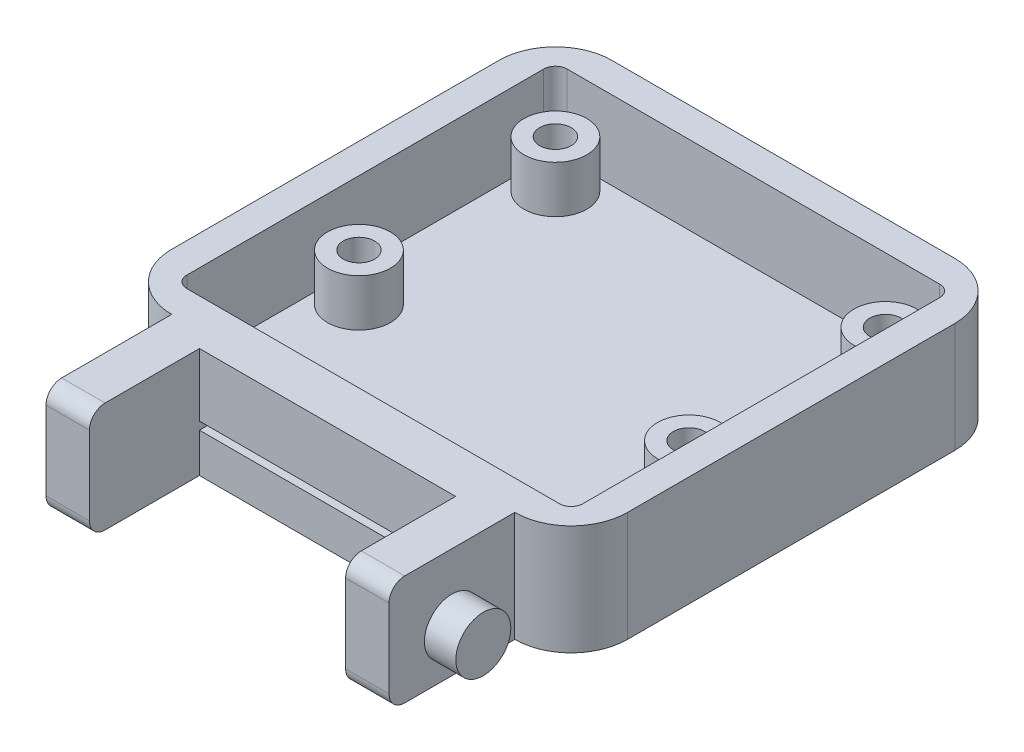
SolidWorks part; units mm, degrees
ref_plane "Front Plane" through (0, 0, 0) normal (0, 0, 1) x (1, 0, 0)
ref_plane "Top Plane" through (0, 0, 0) normal (0, 1, 0) x (1, 0, 0)
ref_plane "Right Plane" through (0, 0, 0) normal (1, 0, 0) x (0, 0, -1)
sketch "Sketch1" plane through (0, 0, 0) normal (0, 1, 0) x (1, 0, 0)
  line L0 (-12.9215, 14.3928) -> (-12.9215, -6.4335)
  line L1 (-9.3347, 17.9797) -> (12.4917, 17.9797)
  line L2 (16.0785, 14.3928) -> (16.0785, -6.4335)
  line L3 (12.4917, -10.0203) -> (-9.3347, -10.0203)
  arc A0 (-12.9215, 14.3928) -> (-9.3347, 17.9797) centre (-9.3347, 14.3928) cw
  arc A1 (12.4917, 17.9797) -> (16.0785, 14.3928) centre (12.4917, 14.3928) cw
  arc A2 (-12.9215, -6.4335) -> (-9.3347, -10.0203) centre (-9.3347, -6.4335) ccw
  arc A3 (16.0785, -6.4335) -> (12.4917, -10.0203) centre (12.4917, -6.4335) cw
  point P12 (13.3502, -6.731)
  point P13 (10.2345, 13.1228)
  point P14 (-14.244, -6.1966)
  point P15 (13.2342, -7.4419)
  point P16 (13.2944, -7.6806)
  point P17 (14.1323, -8.0157)
  point P18 (16.4783, -7.5114)
  point P19 (-10.5014, -10.8645)
  point P20 (16.0873, -8.6844)
  point P21 (16.2549, -8.6753)
  point P22 (-12.4565, 12.2051)
  point P23 (-12.0096, -7.3454)
  dimension "D1" = 29
  dimension "D2" = 28
extrude "Boss-Extrude1" add sketch "Sketch1" along normal blind 7
sketch "Sketch2" plane through (0, 7, 0) normal (0, 1, 0) x (1, 0, 0)
  line L0 (-10.2745, 16.0797) -> (13.4314, 16.0797)
  line L1 (14.1785, 15.3326) -> (14.1785, -7.3733)
  line L2 (13.4314, -8.1203) -> (-10.2745, -8.1203)
  line L4 (-8.9215, 13.9797) -> (12.0785, 13.9797) construction
  line L5 (1.5785, 16.0797) -> (1.5785, -8.1203) construction
  line L6 (-11.0215, -7.3733) -> (-11.0215, 15.3326)
  line L7 (12.4917, 17.9797) -> (-9.3347, 17.9797) construction
  line L8 (16.0785, -6.4335) -> (16.0785, 14.3928) construction
  circle A0 centre (-8.9215, 13.9797) radius 2
  circle A1 centre (12.0785, 13.9797) radius 2
  circle A2 centre (-8.9215, 1.4797) radius 2
  circle A3 centre (12.0785, 1.4797) radius 2
  arc A4 (-10.2745, 16.0797) -> (-11.0215, 15.3326) centre (-10.2745, 15.3326) ccw
  arc A5 (13.4314, 16.0797) -> (14.1785, 15.3326) centre (13.4314, 15.3326) cw
  arc A6 (14.1785, -7.3733) -> (13.4314, -8.1203) centre (13.4314, -7.3733) cw
  arc A7 (-10.2745, -8.1203) -> (-11.0215, -7.3733) centre (-10.2745, -7.3733) cw
  point P22 (0, 0)
  point P23 (0, 0)
  point P24 (0, 0)
  point P25 (1.5785, 13.9797)
  point P26 (0, 0)
  point P31 (-9.6321, 16.0797)
  point P32 (13.4314, -8.1203)
  dimension "D5" = 1.9
  dimension "D7" = 4
  dimension "D1" = 21
  dimension "D2" = 12.5
  dimension "D3" = 24.2
  dimension "D4" = 25.2
  dimension "D6" = 1.9
  dimension "D8" = 2.1
extrude "Cut-Extrude2" cut sketch "Sketch2" against normal blind 5
sketch "Sketch3" plane through (0, 7, 0) normal (0, 1, 0) x (1, 0, 0)
  circle A0 centre (12.0785, 13.9797) radius 2
  circle A1 centre (12.0785, 1.4797) radius 2
  circle A2 centre (-8.9215, 13.9797) radius 2
  circle A3 centre (-8.9215, 1.4797) radius 2
extrude "Cut-Extrude3" cut sketch "Sketch3" against normal blind 2
sketch "Sketch4" plane through (0, 0, 10.0203) normal (0, 0, 1) x (1, 0, 0)
  line L0 (-9.3347, 7) -> (12.4917, 7) construction
  line L1 (9.7285, 3) -> (-6.5715, 3)
  line L2 (9.7285, 3) -> (9.7285, 2.5)
  line L3 (9.7285, 2.5) -> (-6.5715, 2.5)
  line L4 (-6.5715, 3) -> (-6.5715, 2.5)
  line L5 (1.5785, 7) -> (1.5785, 0) construction
  line L6 (-9.3347, 0) -> (12.4917, 0) construction
  point P10 (1.5785, 3)
  dimension "D1" = 4
  dimension "D2" = 16.3
  dimension "D3" = 0.5
extrude "Cut-Extrude4" cut sketch "Sketch4" against normal blind 2
hole_wizard "Ø2.0mm Dowel Hole1" positions "Sketch5" profile "Sketch6" hole size "Ø2.0" standard "ANSI Metric" end condition through all
sketch "Sketch5" plane through (0, 5, 0) normal (0, 1, 0) x (1, 0, 0)
  point P0 (12.0785, 1.4797)
  point P3 (12.0785, 13.9797)
  point P6 (-8.9215, 1.4797)
  point P9 (-8.9215, 13.9797)
sketch "Sketch6" plane through (12.0785, 5, -1.4797) normal (1, 0, 0) x (0, 0, 1)
  line L0 (0, 0) -> (0, 5)
  line L1 (0, 5) -> (1, 5)
  line L2 (1, 5) -> (1, 0)
  line L5 (1, 0) -> (0, 0)
  line L11 (0, -6.35) -> (0, 107.95) construction
  dimension "Thru Hole Dia." = 2
  dimension "Thru Hole Depth" = 5
sketch "Sketch8" plane through (0, 0, 10.0203) normal (0, 0, 1) x (1, 0, 0)
  line L1 (-6.5715, 3) -> (9.7285, 3)
  line L2 (-6.5715, 3) -> (-6.5715, 2.5)
  line L3 (-6.5715, 2.5) -> (9.7285, 2.5)
  line L4 (9.7285, 3) -> (9.7285, 2.5)
  line L5 (-9.3347, 7) -> (12.4917, 7)
  line L6 (-9.3347, 7) -> (-9.3347, 0)
  line L7 (-9.3347, 0) -> (12.4917, 0)
  line L8 (12.4917, 7) -> (12.4917, 0)
extrude "Boss-Extrude2" add sketch "Sketch8" along normal blind 8
sketch "Sketch9" plane through (12.4917, 0, 0) normal (1, 0, 0) x (0, 0, -1)
  line L0 (-18.0203, 2.5) -> (-18.0203, 3) construction
  line L2 (-10.0203, 7) -> (-10.0203, 0) construction
  circle A0 centre (-14.0203, 2.75) radius 1.75
  point P2 (0, 0)
  point P5 (-18.0203, 2.75)
  point P6 (-15.118, 2.75)
  dimension "D1" = 3.5
  dimension "D2" = 4
extrude "Boss-Extrude3" add sketch "Sketch9" along normal blind 2
pattern_linear "LPattern4" count 2 spacing 23.75 along (-1, 0, 0) of "Boss-Extrude3"
sketch "Sketch10" plane through (0, 0, 18.0203) normal (0, 0, 1) x (1, 0, 0)
  line L0 (12.4917, 7) -> (-9.3347, 7) construction
  line L1 (-6.5715, 7) -> (9.7285, 7)
  line L2 (-6.5715, 7) -> (-6.5715, 0)
  line L3 (-6.5715, 0) -> (9.7285, 0)
  line L4 (9.7285, 7) -> (9.7285, 0)
  line L5 (-9.3347, 0) -> (12.4917, 0) construction
extrude "Cut-Extrude5" cut sketch "Sketch10" against normal blind 7
fillet "Fillet1" radius 1 4 edges at (11.1101, 0, 18.0203) (-7.9531, 0, 18.0203) (11.1101, 7, 18.0203) (-7.9531, 7, 18.0203)
